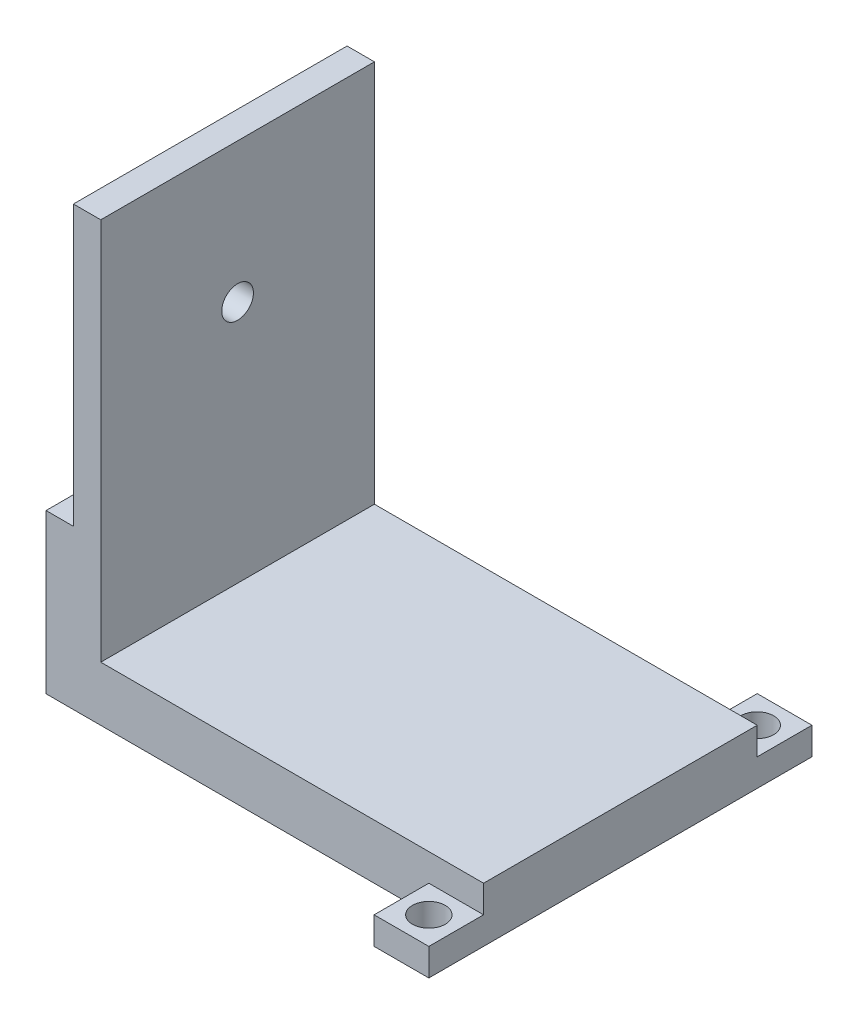
SolidWorks part; units mm, degrees
ref_plane "Front Plane" through (0, 0, 0) normal (0, 0, 1) x (1, 0, 0)
ref_plane "Top Plane" through (0, 0, 0) normal (0, 1, 0) x (1, 0, 0)
ref_plane "Right Plane" through (0, 0, 0) normal (1, 0, 0) x (0, 0, -1)
sketch "Sketch1" plane through (0, 0, 0) normal (0, 1, 0) x (1, 0, 0)
  line L1 (-2294.3767, 25769.8249) -> (77644.7876, 25769.8249)
  line L2 (-2294.3767, 25769.8249) -> (-2294.3767, -24230.1751)
  line L3 (-2294.3767, -24230.1751) -> (77644.7876, -24230.1751)
  line L4 (77644.7876, 25769.8249) -> (77644.7876, -24230.1751)
  dimension "D1" = 50000
  dimension "D2" = 79939.1644
extrude "Boss-Extrude2" add sketch "Sketch1" along normal blind 10000
sketch "Sketch5" plane through (0, 0, 24230.1751) normal (0, 0, 1) x (1, 0, 0)
  line L0 (-2294.3767, 0) -> (77644.7876, 0) construction
  line L1 (77644.7876, 10000) -> (67647.2264, 10000)
  line L2 (77644.7876, 10000) -> (77644.7876, 0)
  line L3 (77644.7876, 0) -> (67647.2264, 0)
  line L4 (67647.2264, 10000) -> (67647.2264, 0)
extrude "Boss-Extrude3" add sketch "Sketch5" along normal blind 10000
sketch "Sketch6" plane through (0, 10000, 0) normal (0, 1, 0) x (1, 0, 0)
  line L1 (77644.7876, -34230.1751) -> (67647.2264, -34230.1751)
  line L2 (77644.7876, -34230.1751) -> (77644.7876, -24230.1751)
  line L3 (77644.7876, -24230.1751) -> (67647.2264, -24230.1751)
  line L4 (67647.2264, -34230.1751) -> (67647.2264, -24230.1751)
extrude "Cut-Extrude1" cut sketch "Sketch6" against normal blind 5000
sketch "Sketch9" plane through (0, 0, -25769.8249) normal (0, 0, -1) x (-1, 0, 0)
  line L0 (-77644.7876, 10000) -> (2294.3767, 10000) construction
  line L1 (-77644.7876, 0) -> (-67644.7876, 0)
  line L2 (-77644.7876, 0) -> (-77644.7876, 10000)
  line L3 (-77644.7876, 10000) -> (-67644.7876, 10000)
  line L4 (-67644.7876, 0) -> (-67644.7876, 10000)
extrude "Boss-Extrude5" add sketch "Sketch9" along normal blind 10000
sketch "Sketch11" plane through (0, 10000, 0) normal (0, 1, 0) x (1, 0, 0)
  line L1 (77644.7876, 35769.8249) -> (67644.7876, 35769.8249)
  line L2 (77644.7876, 35769.8249) -> (77644.7876, 25769.8249)
  line L3 (77644.7876, 25769.8249) -> (67644.7876, 25769.8249)
  line L4 (67644.7876, 35769.8249) -> (67644.7876, 25769.8249)
extrude "Cut-Extrude3" cut sketch "Sketch11" against normal blind 5000
sketch "Sketch13" plane through (0, 5000, 0) normal (0, 1, 0) x (1, 0, 0)
  circle A0 centre (72646.007, -29230.1751) radius 3000
extrude "Cut-Extrude5" cut sketch "Sketch13" against normal blind 5000
sketch "Sketch14" plane through (0, 5000, 0) normal (0, 1, 0) x (1, 0, 0)
  circle A0 centre (72644.7876, 30769.8249) radius 3000
extrude "Cut-Extrude6" cut sketch "Sketch14" against normal blind 5000
sketch "Sketch15" plane through (0, 10000, 0) normal (0, 1, 0) x (1, 0, 0)
  line L0 (77644.7876, 25769.8249) -> (-2294.3767, 25769.8249) construction
  line L1 (-2294.3767, -24230.1751) -> (7705.6233, -24230.1751)
  line L2 (-2294.3767, -24230.1751) -> (-2294.3767, 25769.8249)
  line L3 (-2294.3767, 25769.8249) -> (7705.6233, 25769.8249)
  line L4 (7705.6233, -24230.1751) -> (7705.6233, 25769.8249)
extrude "Boss-Extrude6" add sketch "Sketch15" along normal blind 70000
sketch "Sketch16" plane through (-2294.3767, 0, 0) normal (-1, 0, 0) x (0, 0, 1)
  line L0 (24230.1751, 80000) -> (24230.1751, 0) construction
  line L1 (-25769.8249, 80000) -> (24230.1751, 80000)
  line L2 (-25769.8249, 80000) -> (-25769.8249, 29000)
  line L3 (-25769.8249, 29000) -> (24230.1751, 29000)
  line L4 (24230.1751, 80000) -> (24230.1751, 29000)
extrude "Cut-Extrude7" cut sketch "Sketch16" against normal blind 5000
sketch "Sketch17" plane through (2705.6233, 0, 0) normal (-1, 0, 0) x (0, 0, 1)
  circle A0 centre (-769.8249, 54500) radius 2894.0246
  point P10 (-84191.2458, 69837.8386)
extrude "Cut-Extrude8" cut sketch "Sketch17" against normal blind 5000
